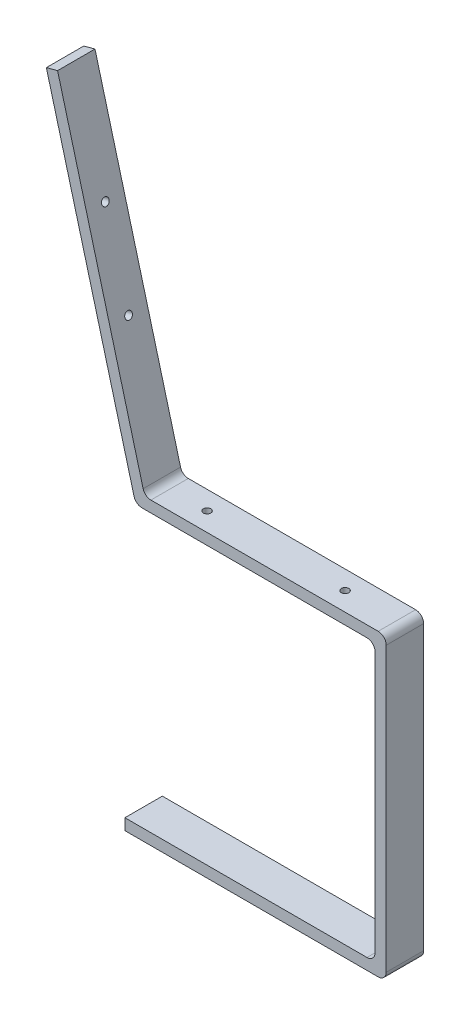
SolidWorks part; units mm, degrees
ref_plane "Front Plane" through (0, 0, 0) normal (0, 0, 1) x (1, 0, 0)
ref_plane "Top Plane" through (0, 0, 0) normal (0, 1, 0) x (1, 0, 0)
ref_plane "Right Plane" through (0, 0, 0) normal (1, 0, 0) x (0, 0, -1)
sketch "Sketch1" plane through (0, 0, 0) normal (0, 0, 1) x (1, 0, 0)
  line L0 (-388.398, -14.1108) -> (-502.7337, 412.5956)
  line L5 (-378.024, -22.0711) -> (-74.2472, -22.0711)
  line L7 (-412.7344, -422.0711) -> (-74.2472, -422.0711)
  line L8 (-63.5072, -32.8111) -> (-63.5072, -411.3311)
  line L9 (-390.1122, -37.0711) -> (-89.2472, -37.0711)
  line L11 (-412.7344, -407.0711) -> (-89.2472, -407.0711)
  line L12 (-78.5072, -47.8111) -> (-78.5072, -396.3311)
  line L13 (-502.7337, 412.5956) -> (-517.7337, 408.5763)
  line L14 (-517.7337, 408.5763) -> (-400.4864, -29.1101)
  line L15 (-412.7344, -422.0711) -> (-412.7344, -407.0711)
  arc A0 (-74.2472, -22.0711) -> (-63.5072, -32.8111) centre (-74.2472, -32.8111) cw
  arc A1 (-378.024, -22.0711) -> (-388.398, -14.1108) centre (-378.024, -11.3311) cw
  arc A2 (-89.2472, -37.0711) -> (-78.5072, -47.8111) centre (-89.2472, -47.8111) cw
  arc A3 (-63.5072, -411.3311) -> (-74.2472, -422.0711) centre (-74.2472, -411.3311) cw
  arc A4 (-89.2472, -407.0711) -> (-78.5072, -396.3311) centre (-89.2472, -396.3311) ccw
  arc A5 (-400.4864, -29.1101) -> (-390.1122, -37.0711) centre (-390.1122, -26.3311) ccw
  point P14 (-63.5072, -22.0711)
  point P21 (-63.5072, -422.0711)
  dimension "D8" = 10.74
  dimension "D9" = 10.74
  dimension "D10" = 10.74
  dimension "D11" = 10.74
  dimension "D12" = 10.74
  dimension "D1" = 15
  dimension "D2" = 15
  dimension "D3" = 400
  dimension "D4" = 15
  dimension "D5" = 105
  dimension "D6" = 15
  dimension "D7" = 0.004
extrude "Boss-Extrude1" add sketch "Sketch1" along normal mid plane 50 contours L9 A2 L12 A4 L11 L15 L7 A3 L8 A0 L5 A1 L0 L13 L14 A5
sketch "Sketch2" plane through (-365.908, -98.0448, 0) normal (0.9659, 0.2588, 0) x (0, 0, -1)
  line L0 (-330.5386, 378.6538) -> (405.1165, 378.6538) construction
  line L1 (405.1165, 258.6538) -> (-330.5386, 258.6538) construction
  line L2 (0, 616.7845) -> (0, 36.608) construction
  line L3 (-25, 528.6538) -> (25, 528.6538) construction
  circle A0 centre (0, 378.6538) radius 5
  circle A1 centre (0, 258.6538) radius 5
  dimension "D1" = 150
  dimension "D2" = 120
sketch "Sketch3" plane through (0, -22.0711, 0) normal (0, 1, 0) x (1, 0, 0)
  line L0 (-63.5072, 0) -> (-592.4472, 0) construction
  line L1 (-63.5072, -25) -> (-63.5072, 25) construction
  line L2 (-323.5072, 228.1115) -> (-323.5072, -199.4158) construction
  line L3 (-143.5072, 228.1115) -> (-143.5072, -199.4158) construction
  circle A0 centre (-327.9772, 0) radius 5
  circle A1 centre (-143.5072, 0) radius 5
  dimension "D1" = 80
  dimension "D2" = 180
extrude "Cut-Extrude1" cut sketch "Sketch3" against normal blind 20
extrude "Cut-Extrude2" cut sketch "Sketch2" against normal blind 20
